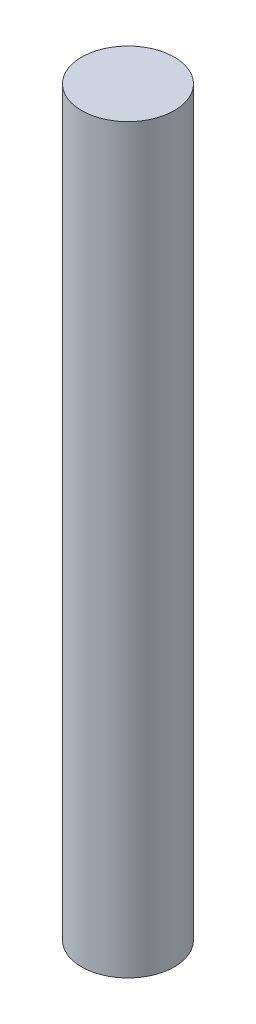
SolidWorks part; units mm, degrees
material "1060 Alloy"
ref_plane "Front Plane" through (0, 0, 0) normal (0, 0, 1) x (1, 0, 0)
ref_plane "Top Plane" through (0, 0, 0) normal (0, 1, 0) x (1, 0, 0)
ref_plane "Right Plane" through (0, 0, 0) normal (1, 0, 0) x (0, 0, -1)
sketch "Sketch1" plane through (0, 0, 0) normal (0, 1, 0) x (1, 0, 0)
  circle A0 centre (0, 0) radius 3.175
  dimension "D1" = 6.35
extrude "Boss-Extrude1" add sketch "Sketch1" along normal blind 50.8
